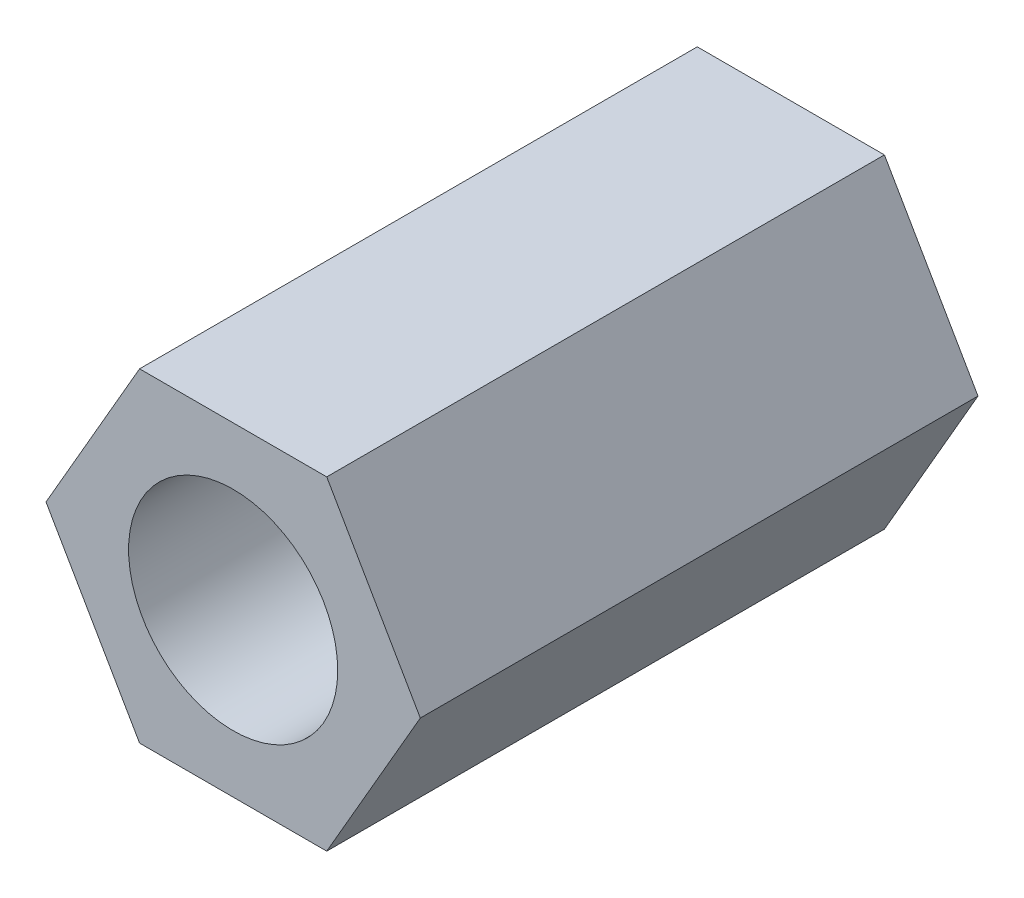
SolidWorks part; units mm, degrees
material "6061-T6 (SS)"
ref_plane "Alzado" through (0, 0, 0) normal (0, 0, 1) x (1, 0, 0)
ref_plane "Planta" through (0, 0, 0) normal (0, 1, 0) x (1, 0, 0)
ref_plane "Vista lateral" through (0, 0, 0) normal (1, 0, 0) x (0, 0, -1)
sketch "Croquis1" plane through (0, 0, 0) normal (0, 0, 1) x (1, 0, 0)
  line L1 (1.3423, -2.325) -> (2.6847, 0)
  line L2 (2.6847, 0) -> (1.3423, 2.325)
  line L3 (1.3423, 2.325) -> (-1.3423, 2.325)
  line L4 (-1.3423, 2.325) -> (-2.6847, 0)
  line L5 (-2.6847, 0) -> (-1.3423, -2.325)
  line L6 (-1.3423, -2.325) -> (1.3423, -2.325)
  circle A0 centre (0, 0) radius 2.325 construction
  circle A1 centre (0, 0) radius 1.5
  dimension "D1" = 3
  dimension "D2" = 4.65
extrude "Saliente-Extruir1" add sketch "Croquis1" along normal blind 8
